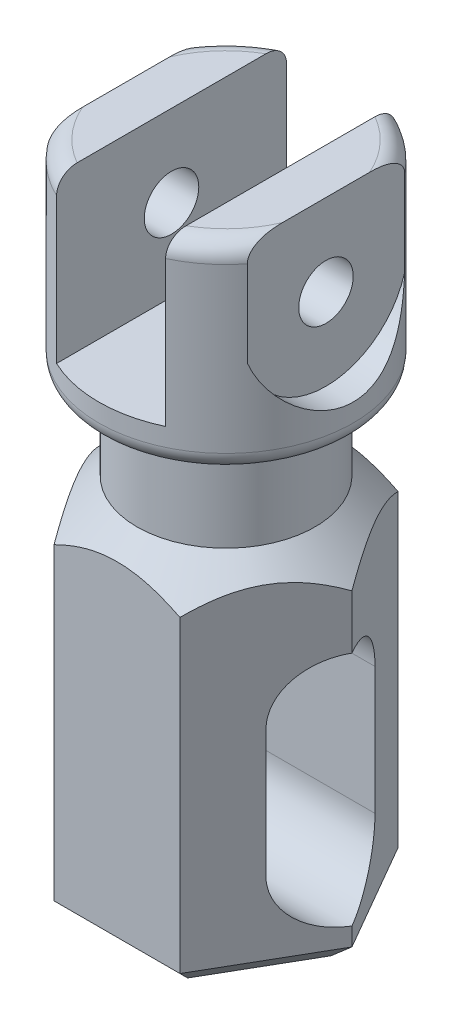
SolidWorks part; units mm, degrees
ref_plane "Front Plane" through (0, 0, 0) normal (0, 0, 1) x (1, 0, 0)
ref_plane "Top Plane" through (0, 0, 0) normal (0, 1, 0) x (1, 0, 0)
ref_plane "Right Plane" through (0, 0, 0) normal (1, 0, 0) x (0, 0, -1)
sketch "Sketch1" plane through (0, 0, 0) normal (0, 1, 0) x (1, 0, 0)
  line L1 (34.641, 0) -> (17.3205, 30)
  line L2 (17.3205, 30) -> (-17.3205, 30)
  line L3 (-17.3205, 30) -> (-34.641, 0)
  line L4 (-34.641, 0) -> (-17.3205, -30)
  line L5 (-17.3205, -30) -> (17.3205, -30)
  line L6 (17.3205, -30) -> (34.641, 0)
  circle A0 centre (0, 0) radius 30 construction
  point P1 (-17.4738, 29.911)
  point P10 (0, 0)
  dimension "D1" = 60
extrude "Boss-Extrude1" add sketch "Sketch1" along normal blind 100
chamfer "Chamfer1" distance 5 angle 45 6 edges at (0, 0, 30) (-25.9808, 0, 15) (-25.9808, 0, -15) (0, 0, -30) (25.9808, 0, -15) (25.9808, 0, 15)
sketch "Sketch2" plane through (0, 0, 0) normal (1, 0, 0) x (0, 0, -1)
  line L0 (0, 60) -> (0, 25) construction
  line L1 (0, 100) -> (0, 5) construction
  line L2 (15, 60) -> (15, 25)
  line L3 (-15, 60) -> (-15, 25)
  line L4 (33, 0) -> (-33, 0) construction
  arc A0 (15, 60) -> (-15, 60) centre (0, 60) ccw
  arc A1 (-15, 25) -> (15, 25) centre (0, 25) ccw
  point P4 (0, 42.5)
  dimension "D3" = 15
  dimension "D1" = 25
  dimension "D2" = 60
extrude "Cut-Extrude1" cut sketch "Sketch2" against normal through all both and the other way through all
sketch "Sketch3" plane through (0, 100, 0) normal (0, 1, 0) x (1, 0, 0)
  circle A0 centre (0, 0) radius 24.5
  dimension "R1" = 49
extrude "Boss-Extrude2" add sketch "Sketch3" along normal blind 25
ref_axis "Axis1" through (0, -6.25, 0) along (0, 1, 0)
sketch "Sketch4" plane through (0, 0, 0) normal (0, 0, 1) x (1, 0, 0)
  line L0 (-24.5, 100) -> (-37.5, 87)
  line L1 (-37.5, 87) -> (-37.5, 100)
  line L2 (-37.5, 100) -> (-24.5, 100)
  dimension "D1" = 45
  dimension "D2" = 13
revolve "Cut-Revolve1" cut sketch "Sketch4" angle 360 about axis through (0, -6.25, 0) along (0, 1, 0)
sketch "Sketch5" plane through (0, 125, 0) normal (0, 1, 0) x (1, 0, 0)
  circle A0 centre (0, 0) radius 35
  dimension "D1" = 70
extrude "Boss-Extrude3" add sketch "Sketch5" along normal blind 55
fillet "Fillet1" radius 5 1 edges at (0, 125, 35)
sketch "Sketch6" plane through (0, 0, 0) normal (0, 0, 1) x (1, 0, 0)
  line L0 (-15, 180) -> (-15, 135)
  line L1 (35, 180) -> (-35, 180) construction
  line L2 (-15, 135) -> (15, 135)
  line L3 (15, 135) -> (15, 180)
  line L4 (15, 180) -> (-15, 180)
  line L5 (0, -6.25) -> (0, 188.2773) construction
  point P4 (0, 180)
  dimension "D1" = 30
  dimension "D2" = 45
extrude "Cut-Extrude2" cut sketch "Sketch6" against normal through all both and the other way through all
ref_plane "Plane1" through (27.5, 0, 0) normal (1, 0, 0) x (0, 0, -1)
sketch "Sketch7" plane through (27.5, 0, 0) normal (1, 0, 0) x (0, 0, -1)
  line L0 (-22.5, 180) -> (22.5, 180)
  line L1 (31.6228, 180) -> (-31.6228, 180) construction
  line L2 (-22.5, 180) -> (-22.5, 157.5)
  line L3 (0, -6.25) -> (0, 188.2773) construction
  line L4 (0, 196.7203) -> (0, 128.0039) construction
  line L5 (22.5, 180) -> (22.5, 157.5)
  arc A0 (-22.5, 157.5) -> (22.5, 157.5) centre (0, 157.5) ccw
  point P11 (0, 156.1994)
  point P14 (0, 180)
  dimension "D1" = 22.5
  dimension "D2" = 22.5
extrude "Cut-Extrude3" cut sketch "Sketch7" along normal through all
mirror "Mirror1" about plane through (0, 0, 0) normal (1, 0, 0) of "Cut-Extrude3"
sketch "Sketch8" plane through (27.5, 0, 0) normal (1, 0, 0) x (0, 0, -1)
  line L0 (0, -6.25) -> (0, 188.2773) construction
  line L1 (21.6506, 180) -> (-21.6506, 180) construction
  circle A0 centre (0, 157.5) radius 7.5
  dimension "D2" = 15
  dimension "D1" = 22.5
extrude "Cut-Extrude4" cut sketch "Sketch8" against normal blind 55
fillet "Fillet2" radius 5 4 edges at (21.8271, 180, -27.3601) (21.8271, 180, 27.3601) (-21.8271, 180, -27.3601) (-21.8271, 180, 27.3601)
sketch "Sketch9" plane through (0, 0, 0) normal (0, -1, 0) x (1, 0, 0)
  circle A0 centre (0, 0) radius 7.5
  dimension "D1" = 15
extrude "Cut-Extrude5" cut sketch "Sketch9" against normal through all
